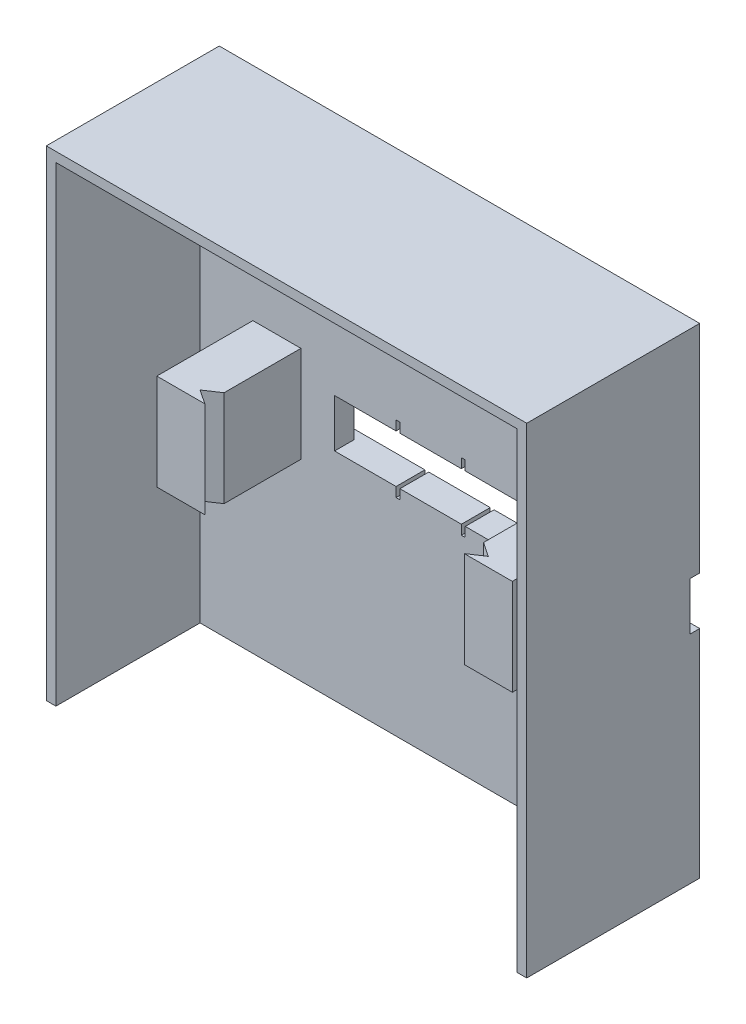
SolidWorks part; units mm, degrees
ref_plane "Přední rovina" through (0, 0, 0) normal (0, 0, 1) x (1, 0, 0)
ref_plane "Horní rovina" through (0, 0, 0) normal (0, 1, 0) x (1, 0, 0)
ref_plane "Pravá rovina" through (0, 0, 0) normal (1, 0, 0) x (0, 0, -1)
sketch "Skica1" plane through (0, 0, 0) normal (0, 0, 1) x (1, 0, 0)
  line L1 (25, 25) -> (-25, 25)
  line L2 (25, 25) -> (25, -25)
  line L3 (25, -25) -> (-25, -25)
  line L4 (-25, 25) -> (-25, -25)
  line L5 (25, 25) -> (-25, -25) construction
  line L6 (25, -25) -> (-25, 25) construction
  point P0 (0, 0)
  point P5 (-27.5, 0)
  point P11 (4.5, 0)
  dimension "D1" = 50
  dimension "D2" = 50
extrude "Přidat vysunutím2" add sketch "Skica1" along normal blind 3 contours L2 L1 L4 L3
sketch "Skica4" plane through (0, 0, 3) normal (0, 0, 1) x (1, 0, 0)
  line L1 (-10, 2.5) -> (10, 2.5)
  line L2 (-10, 2.5) -> (-10, -2.5)
  line L3 (-10, -2.5) -> (10, -2.5)
  line L4 (10, 2.5) -> (10, -2.5)
  line L5 (-10, 2.5) -> (10, -2.5) construction
  line L6 (-10, -2.5) -> (10, 2.5) construction
  line L8 (-25, 25) -> (-25, -25) construction
  point P0 (0, 0)
  dimension "D1" = 5
  dimension "D2" = 20
  dimension "D3" = 15
extrude "Odebrat vysunutím1" cut sketch "Skica4" against normal blind 2
sketch "Skica5" plane through (0, 0, 0) normal (0, 0, -1) x (-1, 0, 0)
  line L10 (25, 25) -> (25, -25) construction
  line L11 (-25, 2.5) -> (25, 2.5)
  line L12 (-25, 2.5) -> (-25, -2.5)
  line L13 (-25, -2.5) -> (25, -2.5)
  line L14 (25, 2.5) -> (25, -2.5)
  line L15 (-25, 2.5) -> (25, -2.5) construction
  line L16 (-25, -2.5) -> (25, 2.5) construction
  point P0 (0, 0)
  dimension "D1" = 5
extrude "Odebrat vysunutím3" cut sketch "Skica5" against normal blind 1 contours L11 L14 L13 L12
sketch "Skica10" plane through (0, 0, 3) normal (0, 0, 1) x (1, 0, 0)
  line L5 (-10, 2.5) -> (-10, -2.5) construction
  line L6 (-13.5, 5) -> (-18.5, 5)
  line L7 (13.5, 5) -> (18.5, 5)
  line L8 (13.5, 5) -> (13.5, -5)
  line L9 (13.5, -5) -> (18.5, -5)
  line L10 (18.5, 5) -> (18.5, -5)
  line L11 (13.5, 5) -> (18.5, -5) construction
  line L12 (13.5, -5) -> (18.5, 5) construction
  line L14 (-13.5, 5) -> (-13.5, -5)
  line L15 (-13.5, -5) -> (-18.5, -5)
  line L16 (-18.5, 5) -> (-18.5, -5)
  line L17 (-13.5, 5) -> (-18.5, -5) construction
  line L18 (-13.5, -5) -> (-18.5, 5) construction
  line L19 (10, -2.5) -> (10, 2.5) construction
  point P0 (-16, 0)
  point P5 (16, 0)
  point P10 (-13.5, 0)
  dimension "D1" = 10
  dimension "D2" = 5
  dimension "D3" = 5
  dimension "D4" = 27
  dimension "D5" = 10
  dimension "D6" = 3.5
  dimension "D7" = 3.5
  dimension "D8" = 0
extrude "Přidat vysunutím6" add sketch "Skica10" along normal blind 10
sketch "Skica12" plane through (0, 5, 0) normal (0, 1, 0) x (1, 0, 0)
  line L0 (-13.5, -13) -> (-13.5, -11)
  line L1 (-13.5, -13) -> (-13.5, -3) construction
  line L2 (-13.5, -11) -> (-15, -12)
  line L3 (-15, -12) -> (-13.5, -13)
  line L4 (13.5, -13) -> (13.5, -11)
  line L5 (13.5, -13) -> (13.5, -3) construction
  line L6 (13.5, -11) -> (15, -12)
  line L7 (15, -12) -> (13.5, -13)
  dimension "D2" = 1.5
  dimension "D1" = 2
  dimension "D3" = 1.5
extrude "Odebrat vysunutím6" cut sketch "Skica12" against normal blind 10
sketch "Skica14" plane through (0, 0, 3) normal (0, 0, 1) x (1, 0, 0)
  line L1 (-25, 25) -> (25, 25)
  line L2 (-25, 25) -> (-25, -25)
  line L3 (-25, -25) -> (25, -25)
  line L4 (25, 25) -> (25, -25)
  line L5 (-24, 24) -> (24, 24)
  line L6 (-24, 24) -> (-24, -25)
  line L7 (-24, -25) -> (24, -25)
  line L8 (24, 24) -> (24, -25)
  line M13 (-25, -25) -> (25, -25)
  line M14 (25, -25) -> (25, 25)
  line M15 (25, 25) -> (-25, 25)
  line M16 (-25, 25) -> (-25, -25)
  dimension "D1" = 1
  dimension "D2" = 1
  dimension "D3" = 1
  dimension "D4" = 0
extrude "Přidat vysunutím9" add sketch "Skica14" along normal blind 15 contours L5 L8 L6 M13 M14 M15 M16
sketch "Skica16" plane through (0, 0, 0) normal (0, 0, -1) x (-1, 0, 0)
  line L1 (-3.2, 3.5) -> (-3.6, 3.5)
  line L2 (-3.2, 3.5) -> (-3.2, -3.5)
  line L3 (-3.2, -3.5) -> (-3.6, -3.5)
  line L4 (-3.6, 3.5) -> (-3.6, -3.5)
  line L5 (-3.2, 3.5) -> (-3.6, -3.5) construction
  line L6 (-3.2, -3.5) -> (-3.6, 3.5) construction
  line L8 (-10, -2.5) -> (-10, 2.5) construction
  line L9 (10, 2.5) -> (10, -2.5) construction
  line L10 (3.6, 3.5) -> (3.2, 3.5)
  line L11 (3.6, 3.5) -> (3.6, -3.5)
  line L12 (3.6, -3.5) -> (3.2, -3.5)
  line L13 (3.2, 3.5) -> (3.2, -3.5)
  line L14 (3.6, 3.5) -> (3.2, -3.5) construction
  line L15 (3.6, -3.5) -> (3.2, 3.5) construction
  point P0 (-3.4, 0)
  point P7 (3.4, 0)
  dimension "D1" = 7
  dimension "D2" = 0.4
  dimension "D3" = 6.4
  dimension "D4" = 7
  dimension "D5" = 0.4
  dimension "D6" = 6.4
  dimension "D7" = 6.4
extrude "Odebrat vysunutím7" cut sketch "Skica16" against normal blind 10
sketch "Skica17" plane through (0, 0, 1) normal (0, 0, -1) x (-1, 0, 0)
  line L0 (-25, 2.5) -> (-25, -2.5) construction
  line L1 (-10, -2.5) -> (-10, 2.5) construction
  line L2 (25, 2.5) -> (25, -2.5) construction
  circle A0 centre (-16, 0) radius 2
  circle A1 centre (16, 0) radius 2
  dimension "D1" = 4
  dimension "D2" = 4
  dimension "D3" = 9
  dimension "D4" = 6
  dimension "D5" = 9
extrude "Odebrat vysunutím8" cut sketch "Skica17" against normal blind 4
